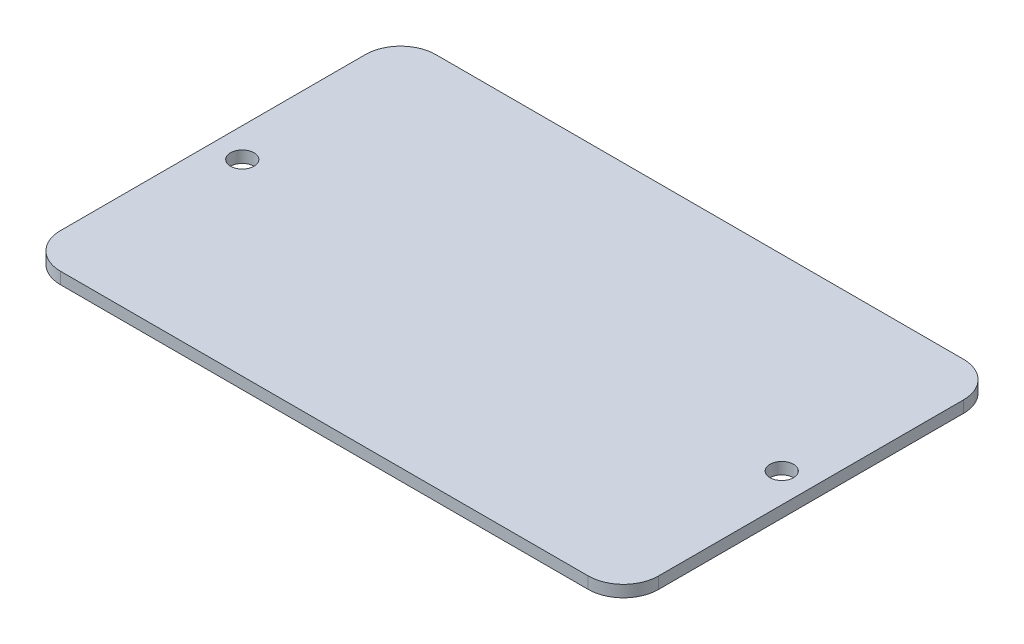
SolidWorks part; units mm, degrees
ref_plane "Front Plane" through (0, 0, 0) normal (0, 0, 1) x (1, 0, 0)
ref_plane "Top Plane" through (0, 0, 0) normal (0, 1, 0) x (1, 0, 0)
ref_plane "Right Plane" through (0, 0, 0) normal (1, 0, 0) x (0, 0, -1)
sketch "Sketch1" plane through (0, 0, 0) normal (0, 1, 0) x (1, 0, 0)
  line L0 (0, 25.4) -> (80.9625, 25.4) construction
  line L1 (0, 0) -> (80.9625, 0)
  line L2 (0, 0) -> (0, 50.8)
  line L3 (0, 50.8) -> (80.9625, 50.8)
  line L4 (80.9625, 0) -> (80.9625, 50.8)
  circle A0 centre (3.9688, 25.4) radius 1.5875
  circle A1 centre (76.9938, 25.4) radius 1.5875
  dimension "D3" = 3.175
  dimension "D1" = 80.9625
  dimension "D2" = 50.8
  dimension "D4" = 3.9688
  dimension "D5" = 3.9688
extrude "Boss-Extrude1" add sketch "Sketch1" along normal blind 1.5875
fillet "Fillet1" radius 4.7625 4 edges at (0, 0.7937, -50.8) (80.9625, 0.7937, -50.8) (80.9625, 0.7937, 0) (0, 0.7937, 0)
